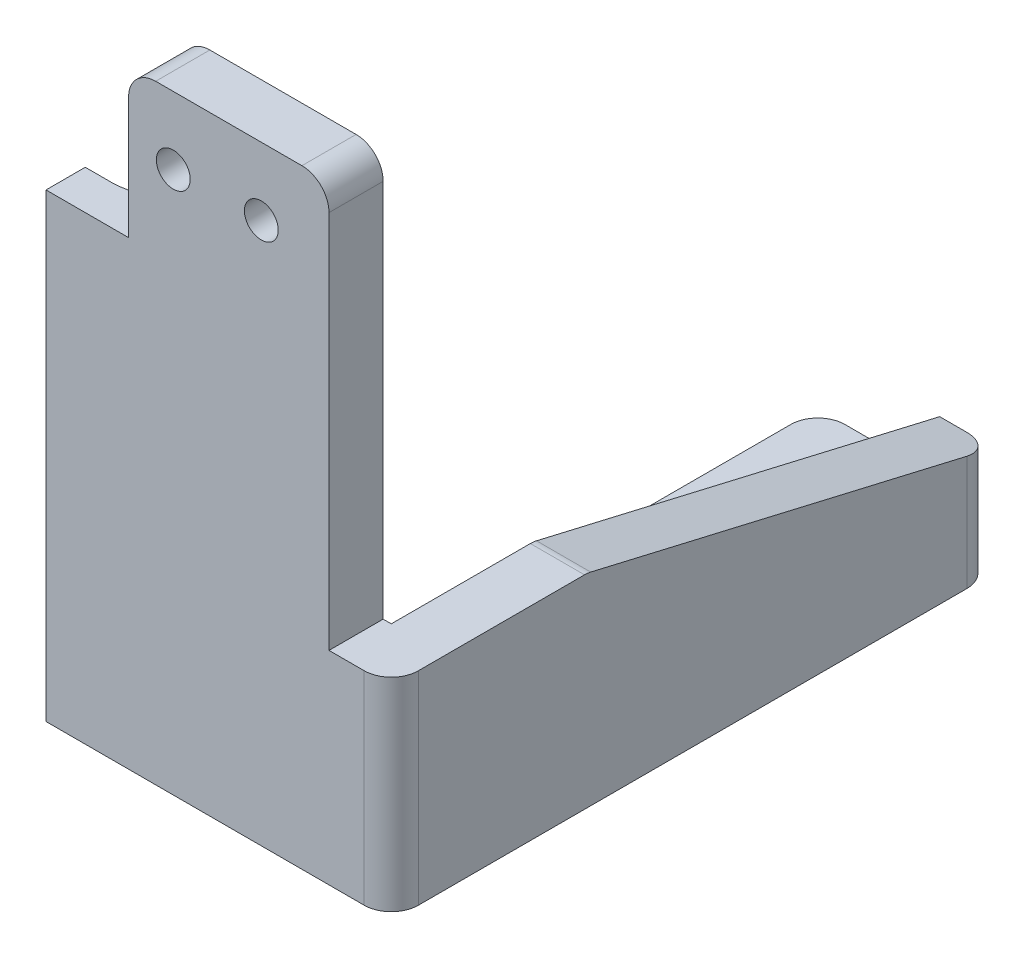
SolidWorks part; units mm, degrees
ref_plane "Front Plane" through (0, 0, 0) normal (0, 0, 1) x (1, 0, 0)
ref_plane "Top Plane" through (0, 0, 0) normal (0, 1, 0) x (1, 0, 0)
ref_plane "Right Plane" through (0, 0, 0) normal (1, 0, 0) x (0, 0, -1)
sketch "Sketch1" plane through (0, 0, 0) normal (0, 0, 1) x (1, 0, 0)
  line L0 (0, 8.4721) -> (0, 0) construction
  line L1 (0, 0) -> (-3.25, 0) construction
  line L3 (-6.55, 5) -> (8.25, 5)
  line L4 (-6.55, 5) -> (-6.55, -40)
  line L5 (-6.55, -40) -> (8.25, -40)
  line L6 (8.25, 5) -> (8.25, -40)
  circle A0 centre (-3.25, 0) radius 1.25
  circle A1 centre (3.25, 0) radius 1.25
  dimension "D1" = 6.5
  dimension "D2" = 2.5
  dimension "D3" = 3.3
  dimension "D4" = 5
  dimension "D5" = 5
  dimension "D6" = 40
extrude "Boss-Extrude1" add sketch "Sketch1" along normal mid plane 4
sketch "Sketch2" plane through (0, -40, 0) normal (0, -1, 0) x (1, 0, 0)
  line L0 (8.25, 2) -> (-6.55, 2) construction
  line L1 (-6.55, 2) -> (-6.55, -2) construction
  line L2 (-10.65, 0.9) -> (-12.65, 0.9) construction
  line L3 (-12.65, -2) -> (-6.55, -2) construction
  line L4 (-6.55, -2) -> (-6.55, 2)
  line L5 (8.25, -2) -> (-6.55, -2) construction
  line L6 (-12.65, 0.9) -> (-12.65, -2) construction
  line L7 (-6.55, 2) -> (0.45, 2) construction
  line L8 (-6.55, 2) -> (8.25, 2) construction
  line L9 (0.45, 2) -> (0.45, 10.9) construction
  line L10 (0.45, 10.9) -> (-12.65, 10.9) construction
  line L11 (-12.65, 10.9) -> (-12.65, 9.1) construction
  line L12 (-12.65, 9.1) -> (-10.65, 9.1) construction
  line L13 (0, 0) -> (12.4243, 0) construction
  line L14 (-12.65, -9.1) -> (-10.65, -9.1)
  line L15 (-12.65, -10.9) -> (-12.65, -9.1)
  line L16 (0.45, -10.9) -> (-12.65, -10.9)
  line L17 (0.45, -2) -> (0.45, -10.9)
  line L18 (-6.55, -2) -> (0.45, -2)
  line L19 (-12.65, -0.9) -> (-12.65, 2)
  line L20 (-12.65, 2) -> (-6.55, 2)
  line L21 (-10.65, -0.9) -> (-12.65, -0.9)
  arc A0 (-10.65, 0.9) -> (-10.65, 9.1) centre (-10.65, 5) ccw construction
  arc A1 (-10.65, -0.9) -> (-10.65, -9.1) centre (-10.65, -5) cw
  dimension "D1" = 8.2
  dimension "D3" = 4.1
  dimension "D2" = 3
  dimension "D4" = 2
  dimension "D5" = 2
  dimension "D6" = 1.8
  dimension "D7" = 7
extrude "Boss-Extrude2" add sketch "Sketch2" against normal blind 34
chamfer "Chamfer2" distance 5 angle 45 1 edges at (0.45, -23, -10.9)
sketch "Sketch3" plane through (0, -40, 0) normal (0, -1, 0) x (1, 0, 0)
  line L0 (4.35, -37.5) -> (4.35, -6.5) construction
  line L1 (-12.65, 2) -> (8.25, 2) construction
  line L2 (-0.15, -42.5) -> (8.85, -42.5)
  line L3 (-0.15, -42.5) -> (-0.15, 2)
  line L4 (-0.15, 2) -> (8.85, 2)
  line L5 (8.85, -42.5) -> (8.85, 2)
  line L6 (-0.15, -42.5) -> (8.85, 2) construction
  line L7 (-0.15, 2) -> (8.85, -42.5) construction
  circle A0 centre (4.35, -37.5) radius 1.75
  circle A1 centre (4.35, -6.5) radius 1.75
  arc A2 (-10.65, -9.1) -> (-10.65, -0.9) centre (-10.65, -5) ccw construction
  point P7 (4.35, -20.25)
  dimension "D1" = 3.5
  dimension "D2" = 3.5
  dimension "D5" = 15
  dimension "D4" = 1.5
  dimension "D3" = 31
  dimension "D6" = 9
  dimension "D7" = 5
extrude "Boss-Extrude3" add sketch "Sketch3" against normal blind 4
sketch "Sketch4" plane through (0, -40, 0) normal (0, 1, 0) x (-1, 0, 0)
  line L0 (-8.25, 2) -> (-8.25, -2) construction
  line L1 (-8.85, -42.5) -> (-12.85, -42.5)
  line L2 (-8.85, -42.5) -> (-8.85, -2)
  line L3 (-8.85, 2) -> (-12.85, 2)
  line L4 (-12.85, -42.5) -> (-12.85, 2)
  line L5 (-8.25, -2) -> (-8.85, -2)
  line L6 (-8.25, -2) -> (-8.25, 2)
  line L7 (-8.25, 2) -> (-8.85, 2)
  line L8 (-8.25, -2) -> (-0.45, -2) construction
  dimension "D1" = 0
  dimension "D2" = 0
  dimension "D3" = 4
extrude "Boss-Extrude4" add sketch "Sketch4" along normal blind 15
chamfer "Chamfer3" distance 7 distance2 30 1 edges at (10.85, -25, -42.5)
fillet "Fillet3" radius 2 4 edges at (10.85, -25, -12.5) (12.85, -32.5, 2) (12.85, -36, -42.5) (-0.15, -38, -42.5)
fillet "Fillet4" radius 2 2 edges at (8.25, 5, 0) (-6.55, 5, 0)
